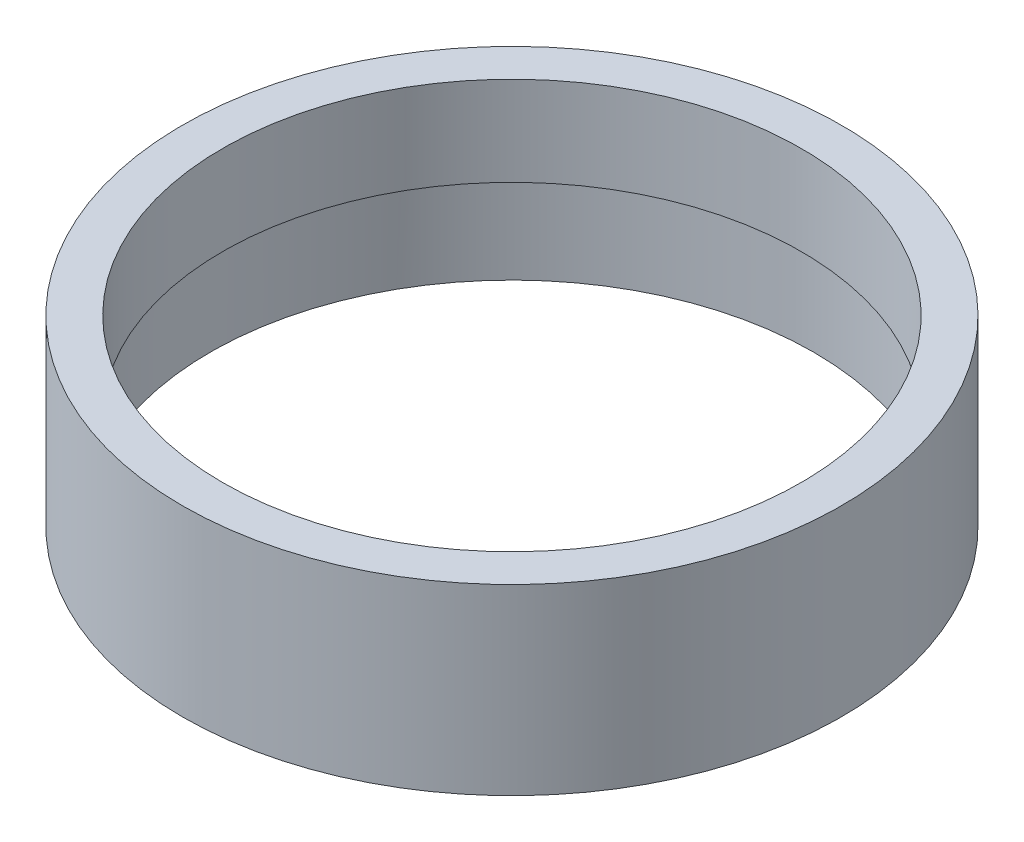
SolidWorks part; units mm, degrees
ref_plane "Front Plane" through (0, 0, 0) normal (0, 0, 1) x (1, 0, 0)
ref_plane "Top Plane" through (0, 0, 0) normal (0, 1, 0) x (1, 0, 0)
ref_plane "Right Plane" through (0, 0, 0) normal (1, 0, 0) x (0, 0, -1)
sketch "Sketch1" plane through (0, 0, 0) normal (0, 1, 0) x (1, 0, 0)
  circle A0 centre (0, 0) radius 77.5
  dimension "D1" = 155
ref_plane "Plane1" through (0, 22, 0) normal (0, 1, 0) x (1, 0, 0)
extrude "Boss-Extrude1" add sketch "Sketch1" along normal blind 43
sketch "Sketch3" plane through (0, 0, 0) normal (0, -1, 0) x (1, 0, 0)
  circle A0 centre (0, 0) radius 71
  dimension "D1" = 142
extrude "Cut-Extrude1" cut sketch "Sketch3" against normal through all
sketch "Sketch4" plane through (0, 22, 0) normal (0, 1, 0) x (1, 0, 0)
  circle A0 centre (0, 0) radius 68.0443
  circle A1 centre (0, 0) radius 71
extrude "Boss-Extrude3" add sketch "Sketch4" along normal through all
